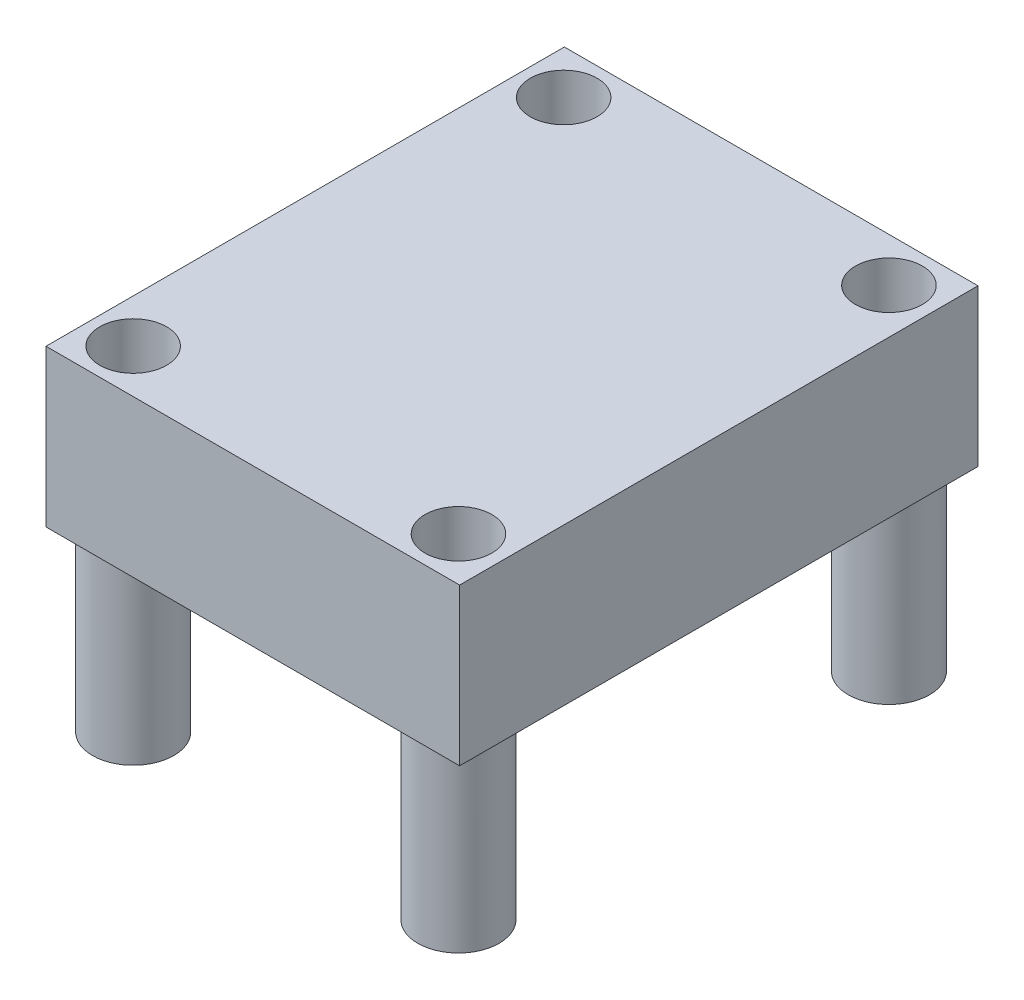
SolidWorks part; units mm, degrees
ref_plane "Front Plane" through (0, 0, 0) normal (0, 0, 1) x (1, 0, 0)
ref_plane "Top Plane" through (0, 0, 0) normal (0, 1, 0) x (1, 0, 0)
ref_plane "Right Plane" through (0, 0, 0) normal (1, 0, 0) x (0, 0, -1)
sketch "Sketch1" plane through (0, 0, 0) normal (0, 1, 0) x (1, 0, 0)
  line L1 (-9.1394, 8.063) -> (11.1298, 8.063)
  line L2 (-9.1394, 8.063) -> (-9.1394, -17.337)
  line L3 (-9.1394, -17.337) -> (11.1298, -17.337)
  line L4 (11.1298, 8.063) -> (11.1298, -17.337)
  dimension "D1" = 20.2692
  dimension "D2" = 25.4
extrude "Boss-Extrude1" add sketch "Sketch1" along normal blind 7.6708
sketch "Sketch2" plane through (0, 0, 0) normal (0, -1, 0) x (-1, 0, 0)
  circle A0 centre (7.0127, -15.1921) radius 1.9939
  circle A1 centre (-8.9251, -15.1921) radius 1.9939
  circle A2 centre (-8.9251, 5.9025) radius 1.9939
  circle A3 centre (7.0127, 5.9025) radius 1.9939
  circle A4 centre (-8.9251, 5.9025) radius 1.6383
  circle A5 centre (7.0127, 5.9025) radius 1.6383
  circle A6 centre (-8.9251, -15.1921) radius 1.6383
  circle A7 centre (7.0127, -15.1921) radius 1.6383
  point P8 (6.9036, 5.9025)
  point P13 (-9.0342, -15.1921)
  point P15 (7.0127, -15.3012)
  dimension "D1" = 3.9878
  dimension "D2" = 3.2766
extrude "Boss-Extrude2" add sketch "Sketch2" along normal blind 8.7122
sketch "Sketch3" plane through (0, 7.6708, 0) normal (0, 1, 0) x (1, 0, 0)
  circle A0 centre (8.9251, 5.9025) radius 1.6383
  circle A1 centre (-7.0127, 5.9025) radius 1.6383
  circle A2 centre (8.9251, -15.1921) radius 1.6383
  circle A3 centre (-7.0127, -15.1921) radius 1.6383
extrude "Cut-Extrude1" cut sketch "Sketch3" against normal through all both
